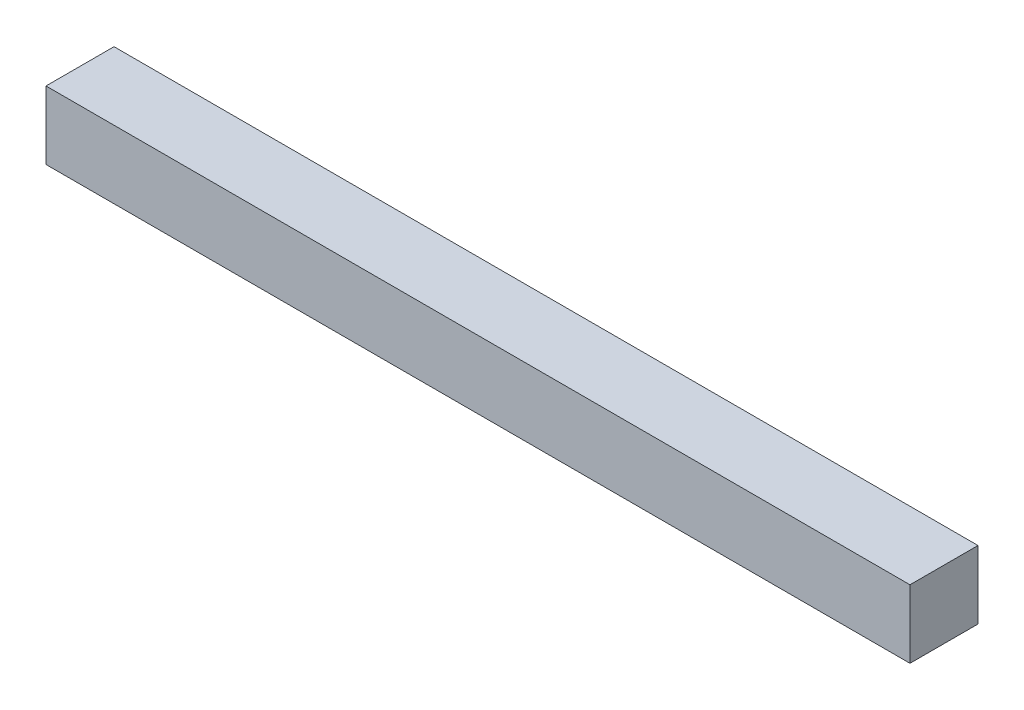
SolidWorks part; units mm, degrees
ref_plane "Plan de face" through (0, 0, 0) normal (0, 0, 1) x (1, 0, 0)
ref_plane "Plan de dessus" through (0, 0, 0) normal (0, 1, 0) x (1, 0, 0)
ref_plane "Plan de droite" through (0, 0, 0) normal (1, 0, 0) x (0, 0, -1)
sketch "Esquisse1" plane through (0, 0, 0) normal (0, 0, 1) x (1, 0, 0)
  line L1 (-14.7006, 5.1608) -> (112.2994, 5.1608)
  line L2 (-14.7006, 5.1608) -> (-14.7006, -4.8392)
  line L3 (-14.7006, -4.8392) -> (112.2994, -4.8392)
  line L4 (112.2994, 5.1608) -> (112.2994, -4.8392)
  dimension "D1" = 10
  dimension "D2" = 127
extrude "Boss.-Extru.1" add sketch "Esquisse1" along normal blind 10 contours L2 L3 L4 L1
equation "\"D2@Esquisse1\"=\"LargeurGauche\" - 23"
equation "\"EpaisseurPlaque\"= 3"
equation "\"ProfondeurBoite\"=460"
equation "\"LongueurSyphon\"=270"
equation "\"LargeurSyphon\"=120"
equation "\"HauteurCoteDroit\"= 490"
equation "\"HauteurCoteGauche\"= 540"
equation "\"HauteurSolSyphon\"= 300"
equation "\"HauteurSyphon\"=\"HauteurCoteGauche\"-\"HauteurSolSyphon\""
equation "\"LargeurDroite\"=10"
equation "\"LargeurGauche\"=150"
equation "\"LargeurBoite\"= \"LargeurDroite\" + \"LargeurGauche\" + \"LargeurSyphon\""
